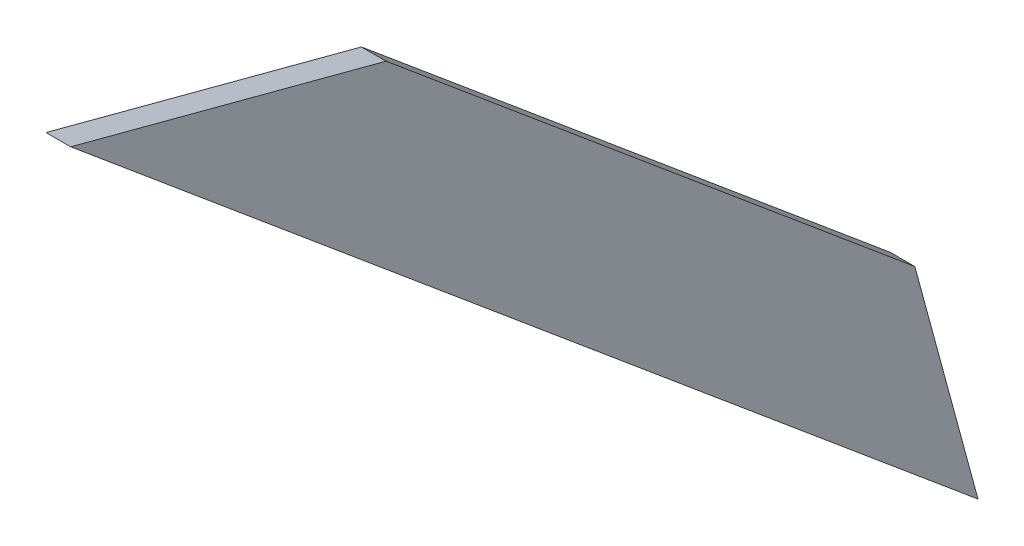
SolidWorks part; units mm, degrees
ref_plane "Front Plane" through (0, 0, 0) normal (0, 0, 1) x (1, 0, 0)
ref_plane "Top Plane" through (0, 0, 0) normal (0, 1, 0) x (1, 0, 0)
ref_plane "Right Plane" through (0, 0, 0) normal (1, 0, 0) x (0, 0, -1)
sketch "Sketch1" plane through (-17.6622, 82.4949, -223.0551) normal (-1, 0, 0) x (0, -1, 0)
  line L4 (-168.1491, 806.7975) -> (-321.8282, 990.5744)
  line L5 (-69.0481, 833.0473) -> (-69.0482, 833.0473) construction
  line L7 (-168.1491, 806.7975) -> (-215.3452, 819.5887)
  line L8 (-321.8282, 990.5744) -> (-304.9067, 926.6907)
  line L9 (-524.6519, 937.885) -> (-282.9481, 1001.9074) construction
  line L10 (-380.014, 772.0622) -> (-275.3795, 1158.1343) construction
  line L11 (-215.3452, 819.5887) -> (-304.9067, 926.6907)
  line L12 (-367.9681, 854.7366) -> (-339.8476, 958.4934) construction
  line L14 (-647.0856, 933.4921) -> (-372.0093, 858.9401) construction
  line L15 (-380.014, 772.0622) -> (-275.3795, 1158.1343) construction
  dimension "D1" = 28
  dimension "D2" = 1
  dimension "D4" = 3
extrude "Boss-Extrude1" add sketch "Sketch1" against normal blind 5
